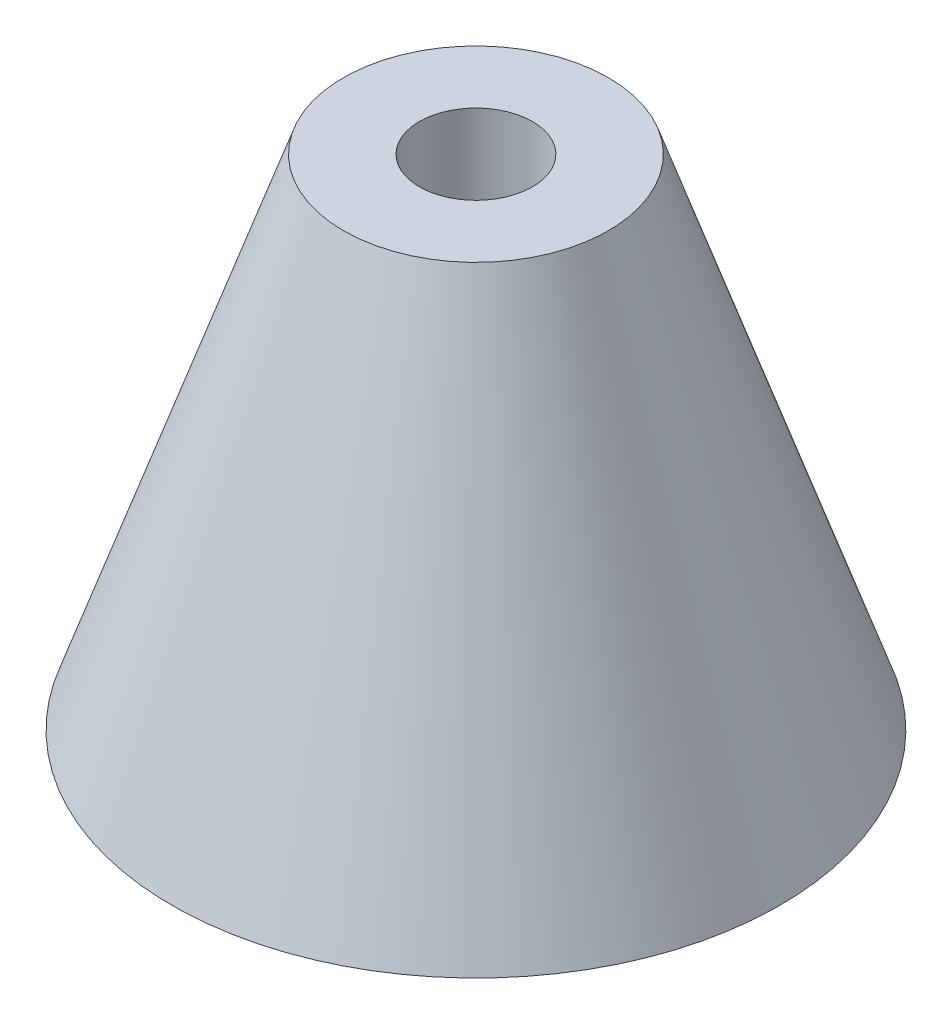
SolidWorks part; units mm, degrees
ref_plane "Front Plane" through (0, 0, 0) normal (0, 0, 1) x (1, 0, 0)
ref_plane "Top Plane" through (0, 0, 0) normal (0, 1, 0) x (1, 0, 0)
ref_plane "Right Plane" through (0, 0, 0) normal (1, 0, 0) x (0, 0, -1)
sketch "Sketch1" plane through (0, 0, 0) normal (0, 0, 1) x (1, 0, 0)
  line L0 (0, 0) -> (0, 20.828)
  line L1 (0, 20.828) -> (2.3622, 20.828)
  line L3 (12.7, 0) -> (2.3622, 0)
  line L4 (2.3622, 0) -> (2.3622, 20.828)
  line L5 (2.3622, 20.828) -> (5.5372, 20.828)
  line L6 (5.5372, 20.828) -> (12.7, 0)
  dimension "D1" = 20.828
  dimension "D2" = 2.3622
  dimension "D3" = 12.7
  dimension "D4" = 3.175
revolve "Revolve1" add sketch "Sketch1" angle 360 about L0
sketch "Sketch2" plane through (0, 0, 0) normal (0, -1, 0) x (1, 0, 0)
  line L1 (0, 5.3819) -> (-4.6609, 2.691)
  line L2 (-4.6609, 2.691) -> (-4.6609, -2.691)
  line L3 (-4.6609, -2.691) -> (0, -5.3819)
  line L4 (0, -5.3819) -> (4.6609, -2.691)
  line L5 (4.6609, -2.691) -> (4.6609, 2.691)
  line L6 (4.6609, 2.691) -> (0, 5.3819)
  circle A0 centre (0, 0) radius 4.6609 construction
  point P1 (-3.4941, 4.0935)
  dimension "D1" = 9.3218
extrude "Cut-Extrude1" cut sketch "Sketch2" against normal blind 3.0988
